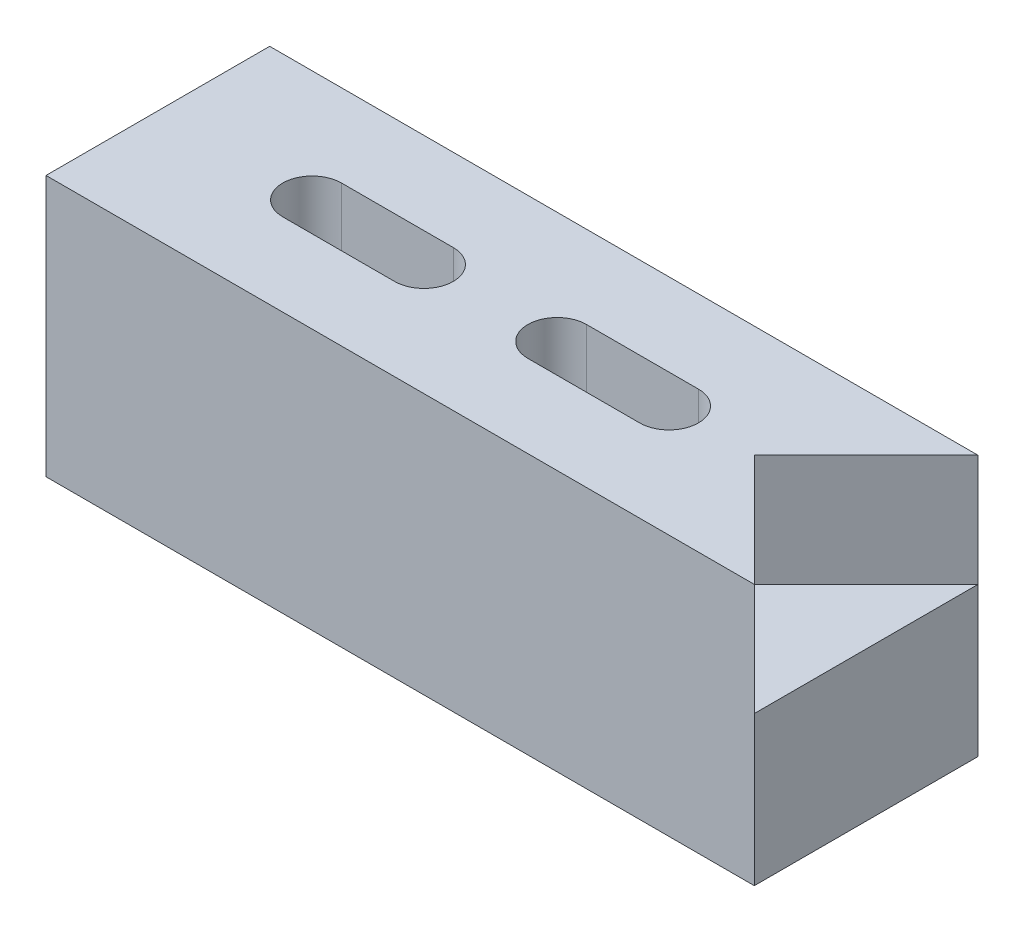
SolidWorks part; units mm, degrees
ref_plane "Front Plane" through (0, 0, 0) normal (0, 0, 1) x (1, 0, 0)
ref_plane "Top Plane" through (0, 0, 0) normal (0, 1, 0) x (1, 0, 0)
ref_plane "Right Plane" through (0, 0, 0) normal (1, 0, 0) x (0, 0, -1)
sketch "Sketch1" plane through (0, 0, 0) normal (0, 0, 1) x (1, 0, 0)
  line L0 (0, 0) -> (48.26, 0)
  line L6 (0, 0) -> (0, 17.78)
  line L10 (0, 17.78) -> (48.26, 17.78)
  line L11 (48.26, 0) -> (48.26, 17.78)
  dimension "D1" = 48.26
  dimension "D2" = 17.78
extrude "Boss-Extrude1" add sketch "Sketch1" against normal blind 15.24
sketch "Sketch3" plane through (0, 17.78, 0) normal (0, 1, 0) x (1, 0, 0)
  line L0 (48.26, 15.24) -> (40.64, 7.62)
  line L1 (40.64, 7.62) -> (48.26, 0)
  line L4 (48.26, 15.24) -> (48.26, 0)
  dimension "D2" = 90
extrude "Cut-Extrude1" cut sketch "Sketch3" against normal blind 7.62
sketch "Sketch4" plane through (0, 17.78, 0) normal (0, 1, 0) x (1, 0, 0)
  line L0 (34.83, 7.62) -> (27.21, 7.62) construction
  line L1 (34.83, 5.62) -> (27.21, 5.62)
  line L2 (34.83, 9.62) -> (27.21, 9.62)
  line L3 (18.13, 7.62) -> (10.51, 7.62) construction
  line L4 (18.13, 5.62) -> (10.51, 5.62)
  line L5 (18.13, 9.62) -> (10.51, 9.62)
  line L6 (48.26, 0) -> (0, 0) construction
  arc A0 (34.83, 5.62) -> (34.83, 9.62) centre (34.83, 7.62) ccw
  arc A1 (27.21, 9.62) -> (27.21, 5.62) centre (27.21, 7.62) ccw
  arc A2 (18.13, 5.62) -> (18.13, 9.62) centre (18.13, 7.62) ccw
  arc A3 (10.51, 9.62) -> (10.51, 5.62) centre (10.51, 7.62) ccw
  point P2 (31.02, 7.62)
  point P7 (14.32, 7.62)
  point P14 (36.83, 7.62)
  point P16 (8.51, 7.62)
  point P18 (20.13, 7.62)
  point P19 (25.21, 7.62)
  dimension "D1" = 4
  dimension "D2" = 3.81
  dimension "D3" = 7.62
  dimension "D4" = 7.62
  dimension "D5" = 5.08
extrude "Cut-Extrude2" cut sketch "Sketch4" against normal through all
